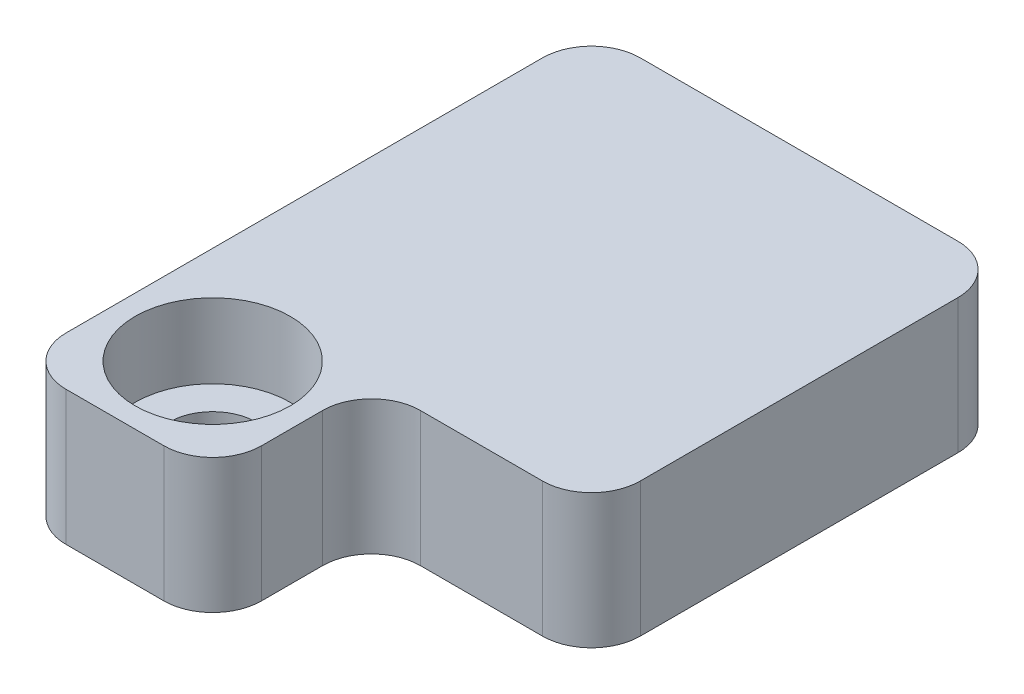
SolidWorks part; units mm, degrees
ref_plane "Front Plane" through (0, 0, 0) normal (0, 0, 1) x (1, 0, 0)
ref_plane "Top Plane" through (0, 0, 0) normal (0, 1, 0) x (1, 0, 0)
ref_plane "Right Plane" through (0, 0, 0) normal (1, 0, 0) x (0, 0, -1)
sketch "Sketch1" plane through (0, 0, 0) normal (0, 1, 0) x (1, 0, 0)
  line L1 (-4.25, -4.25) -> (4.25, -4.25)
  line L2 (-4.25, -4.25) -> (-4.25, 4.25)
  line L3 (-4.25, 4.25) -> (4.25, 4.25)
  line L4 (4.25, -4.25) -> (4.25, 4.25)
  line L5 (-4.25, -4.25) -> (4.25, 4.25) construction
  line L6 (-4.25, 4.25) -> (4.25, -4.25) construction
  point P0 (0, 0)
  dimension "D1" = 8.5
  dimension "D2" = 8.5
extrude "Extrude1" add sketch "Sketch1" along normal blind 2.75
sketch "Sketch8" plane through (0, 0, 0) normal (0, -1, 0) x (1, 0, 0)
  line L17 (-3.9, -3.9) -> (3.9, -3.9)
  line L18 (3.9, -3.9) -> (3.9, 3.9)
  line L19 (3.9, 3.9) -> (-3.9, 3.9)
  line L20 (-3.9, 3.9) -> (-3.9, -3.9)
  line L21 (-3.9, -3.9) -> (3.9, -3.9)
  line L22 (3.9, -3.9) -> (3.9, 3.9)
  line L23 (3.9, 3.9) -> (-3.9, 3.9)
  line L24 (-3.9, 3.9) -> (-3.9, -3.9)
  dimension "D1" = 0.35
extrude "Extrude6" cut sketch "Sketch8" against normal blind 0.5
sketch "Sketch3" plane through (0, 0, 4.25) normal (0, 0, 1) x (1, 0, 0)
  line L0 (-4.25, 0) -> (4.25, 0) construction
  line L1 (-4.25, 2.75) -> (-0.25, 2.75)
  line L2 (-4.25, 2.75) -> (-4.25, 0)
  line L3 (-4.25, 0) -> (-0.25, 0)
  line L4 (-0.25, 2.75) -> (-0.25, 0)
  dimension "D1" = 4
extrude "Extrude3" add sketch "Sketch3" along normal blind 3.25
hole_wizard "CBORE for #0 Socket Head Cap Screw1" positions "3DSketch2" profile "Sketch6" counterbore size "#0" standard "Ansi Inch" end condition through all
sketch3d "3DSketch2"
  line L0 (-0.25, 2.75, 7.5) -> (-4.25, 2.75, 7.5) construction
  line L1 (-0.25, 2.75, 7.5) -> (-0.25, 2.75, 4.25) construction
  point P0 (-2.25, 2.75, 5.5)
  dimension "D1" = 2
  dimension "D2" = 2
sketch "Sketch6" plane through (-2.25, 2.75, 5.5) normal (1, 0, 0) x (0, 0, 1)
  line L0 (0, 0) -> (0, 2.75)
  line L1 (0, 2.75) -> (0.889, 2.75)
  line L3 (0.889, 2.75) -> (0.889, 1.524)
  line L4 (0.889, 1.524) -> (1.5875, 1.524)
  line L5 (1.5875, 1.524) -> (1.5875, 0)
  line L7 (1.5875, 0) -> (0, 0)
  line L11 (0, -6.35) -> (0, 107.95) construction
  dimension "Thru Hole Dia." = 1.778
  dimension "Thru Hole Depth" = 2.75
  dimension "C'Bore Dia." = 3.175
  dimension "C'Bore Depth" = 1.524
fillet "Fillet1" radius 1 10 edges at (-3.9, 0.25, 3.9) (-3.9, 0.25, -3.9) (3.9, 0.25, -3.9) (3.9, 0.25, 3.9) (-4.25, 1.375, -4.25) (4.25, 1.375, -4.25) (4.25, 1.375, 4.25) (-0.25, 1.375, 7.5) (-4.25, 1.375, 7.5)
